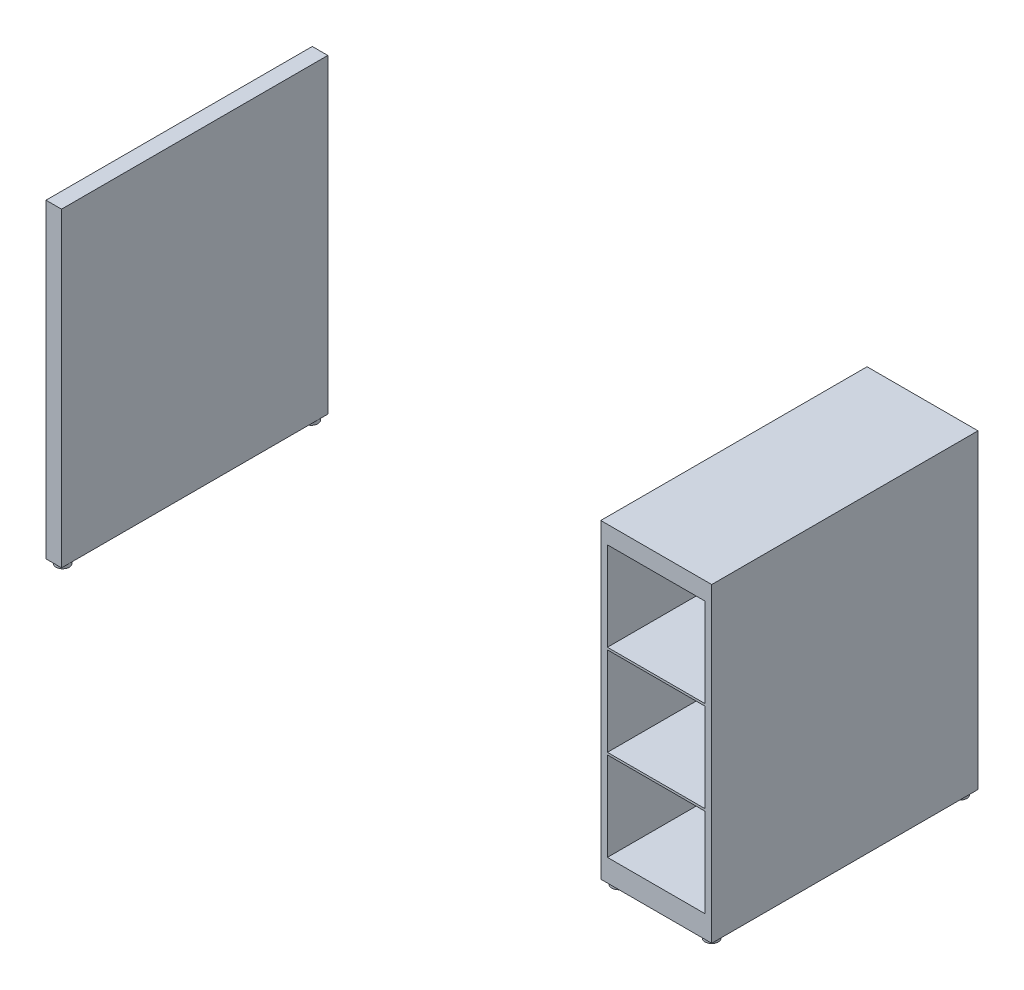
SolidWorks part; units mm, degrees
ref_plane "Front Plane" through (0, 0, 0) normal (0, 0, 1) x (1, 0, 0)
ref_plane "Top Plane" through (0, 0, 0) normal (0, 1, 0) x (1, 0, 0)
ref_plane "Right Plane" through (0, 0, 0) normal (1, 0, 0) x (0, 0, -1)
sketch "Sketch1" plane through (0, 0, 0) normal (0, 1, 0) x (1, 0, 0)
  line L1 (-750, 300) -> (750, 300)
  line L2 (-750, 300) -> (-750, -300)
  line L3 (-750, -300) -> (750, -300)
  line L4 (750, -300) -> (750, 300)
  point P8 (750, 289.4231)
  dimension "D1" = 600
  dimension "D2" = 1500
extrude "Boss-Extrude1" add sketch "Sketch1" along normal blind 700
sketch "Sketch4" plane through (0, 0, 300) normal (0, 0, 1) x (1, 0, 0)
  line L0 (-715, 0) -> (-715, 700)
  line L1 (500, 700) -> (500, 0)
  line L2 (-715, 700) -> (500, 700)
  line L3 (500, 0) -> (-715, 0)
  dimension "D1" = 35
  dimension "D2" = 250
extrude "Cut-Extrude2" cut sketch "Sketch4" against normal blind 750
sketch "Sketch5" plane through (0, 0, 300) normal (0, 0, 1) x (1, 0, 0)
  line L0 (515, 660) -> (515, 460.0999)
  line L2 (515, 455.0999) -> (515, 255.0999)
  line L3 (515, 250.0999) -> (515, 50.0999)
  line L4 (515, 660) -> (735.0006, 660.0999)
  line L5 (735.0006, 660.0999) -> (735.0006, 460.0999)
  line L7 (735.0006, 455.0999) -> (735.0006, 255.0999)
  line L9 (735.0006, 250.0999) -> (735.0006, 50.0999)
  line L10 (735.0006, 50.0999) -> (515, 50.0999)
  line L12 (735.0006, 460.0999) -> (515, 460.0999)
  line L13 (735.0006, 455.0999) -> (515, 455.0999)
  line L14 (735.0006, 255.0999) -> (515, 255.0999)
  line L15 (735.0006, 250.0999) -> (515, 250.0999)
  dimension "D5" = 200
  dimension "D6" = 5
  dimension "D7" = 200
  dimension "D9" = 200
extrude "Cut-Extrude3" cut sketch "Sketch5" against normal blind 580
sketch "Sketch6" plane through (0, 0, 0) normal (0, -1, 0) x (-1, 0, 0)
  line L0 (750, -300) -> (715, -300) construction
  line L1 (715, 300) -> (750, 300) construction
  line L2 (-500, -300) -> (-750, -300) construction
  line L3 (-500, -300) -> (-500, 300) construction
  line L4 (-750, 300) -> (-500, 300) construction
  line L5 (-750, -300) -> (-750, 300) construction
  circle A0 centre (732.5, -280) radius 15
  circle A1 centre (732.5, 280) radius 15
  circle A2 centre (-520, -280) radius 15
  circle A3 centre (-520, 280) radius 15
  circle A4 centre (-730, 280) radius 15
  circle A5 centre (-730, -280) radius 15
  dimension "D1" = 30
  dimension "D3" = 30
  dimension "D5" = 30
  dimension "D8" = 30
  dimension "D11" = 30
  dimension "D14" = 30
  dimension "D2" = 20
  dimension "D4" = 20
  dimension "D6" = 20
  dimension "D7" = 20
  dimension "D9" = 20
  dimension "D10" = 20
  dimension "D12" = 20
  dimension "D13" = 20
  dimension "D15" = 20
  dimension "D16" = 20
extrude "Boss-Extrude3" add sketch "Sketch6" along normal blind 10
